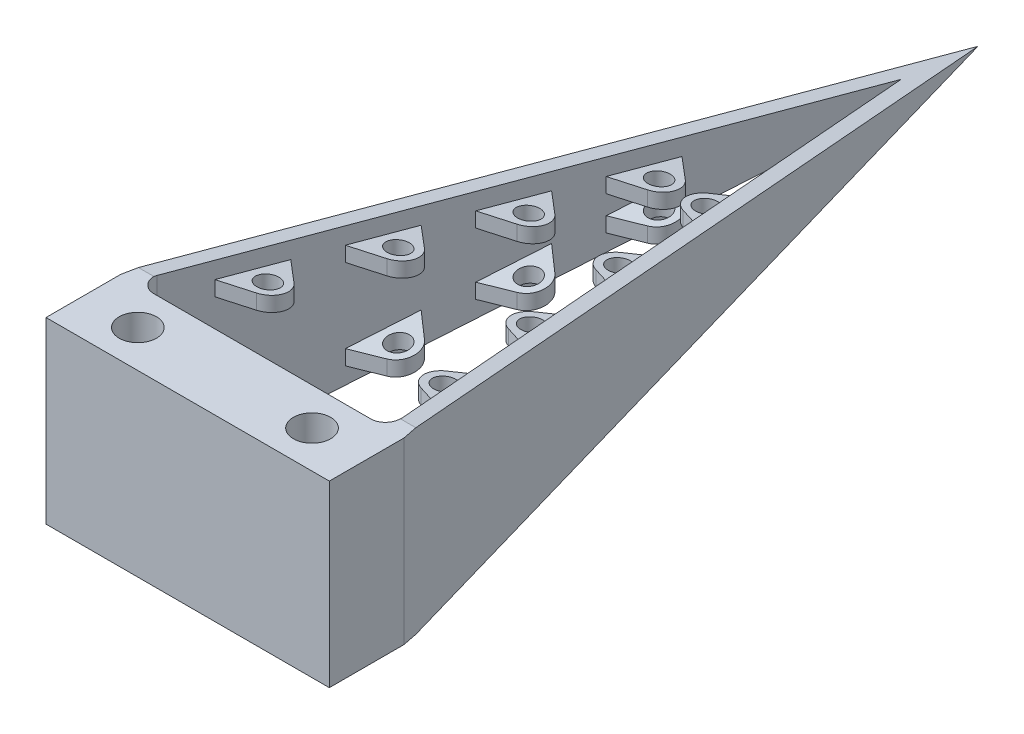
SolidWorks part; units mm, degrees
ref_plane "Front Plane" through (0, 0, 0) normal (0, 0, 1) x (1, 0, 0)
ref_plane "Top Plane" through (0, 0, 0) normal (0, 1, 0) x (1, 0, 0)
ref_plane "Right Plane" through (0, 0, 0) normal (1, 0, 0) x (0, 0, -1)
sketch "Sketch1" plane through (0, 0, 0) normal (0, 1, 0) x (1, 0, 0)
  line L0 (0, 152.4) -> (-30.1625, 0)
  line L1 (-30.1625, 0) -> (-30.1625, -15.875)
  line L2 (-30.1625, -15.875) -> (30.1625, -15.875)
  line L3 (30.1625, -15.875) -> (30.1625, 0)
  line L4 (30.1625, 0) -> (0, 152.4)
  line L5 (-30.1625, 0) -> (30.1625, 0) construction
  line L6 (0, 152.4) -> (0, 0) construction
  line L7 (-30.1625, -7.9375) -> (30.1625, -7.9375) construction
  line L8 (-26.9259, 0) -> (26.9259, 0)
  line L9 (26.9259, 0) -> (0, 136.0467)
  line L10 (0, 136.0467) -> (-26.9259, 0)
  circle A0 centre (-18.542, -7.9375) radius 3.9688
  circle A1 centre (18.542, -7.9375) radius 3.9688
  dimension "D1" = 7.9375
  dimension "D2" = 18.542
  dimension "D3" = 11.6205
  dimension "D4" = 7.9375
  dimension "D5" = 152.4
  dimension "D6" = 3.175
extrude "Boss-Extrude1" add sketch "Sketch1" along normal blind 34.925 and the other way blind 3.175
ref_plane "Plane1" through (0, 15.875, 0) normal (0, 1, 0) x (1, 0, 0)
fillet "Fillet1" radius 3.175 2 edges at (26.9259, 15.875, 0) (-26.9259, 15.875, 0)
sketch "Sketch2" plane through (0, 0, 0) normal (1, 0, 0) x (0, 0, -1)
  line L0 (3.175, 34.925) -> (152.4, 34.925)
  line L1 (0, 34.925) -> (152.4, 34.925) construction
  line L2 (152.4, 34.925) -> (152.4, 15.875)
  line L3 (152.4, -3.175) -> (152.4, 34.925) construction
  line L4 (152.4, 15.875) -> (3.175, 34.925)
  line L5 (3.175, -3.175) -> (152.4, -3.175)
  line L6 (0, -3.175) -> (152.4, -3.175) construction
  line L7 (152.4, -3.175) -> (152.4, 15.875)
  line L8 (3.175, -3.175) -> (152.4, 15.875)
  line L9 (0, -3.175) -> (0, 34.925) construction
  dimension "D1" = 3.175
extrude "Cut-Extrude1" cut sketch "Sketch2" against normal through all both and the other way through all contours L4 L2 L0 | L8 L5 L7
ref_plane "Plane2" through (0, 0, 0) normal (0, -0.9919, -0.1266) x (-1, 0, 0)
sketch "Sketch3" plane through (0, 0, 0) normal (0, -0.9919, -0.1266) x (-1, 0, 0)
  line L0 (-26.1755, 3.3688) -> (0, 136.6974) construction
  line L1 (-16.2187, 23.1834) -> (-24.1614, 30.114)
  line L2 (-17.543, 16.4381) -> (-27.5164, 13.0248)
  line L3 (-22.9287, 36.3928) -> (-19.5737, 53.482)
  line L4 (-24.1614, 30.114) -> (-27.5164, 13.0248)
  line L5 (-29.5341, 2.7474) -> (0, 153.1834) construction
  line L6 (-18.341, 59.7608) -> (-14.986, 76.85)
  line L7 (-13.7534, 83.1288) -> (-10.3984, 100.218)
  line L8 (-11.631, 46.5514) -> (-19.5737, 53.482)
  line L9 (-12.9553, 39.8061) -> (-22.9287, 36.3928)
  line L10 (-8.3676, 63.1741) -> (-18.341, 59.7608)
  line L11 (-14.986, 76.85) -> (-7.0433, 69.9194)
  line L12 (-13.7534, 83.1288) -> (-3.7799, 86.5421)
  line L13 (-10.3984, 100.218) -> (-2.4556, 93.2874)
  arc A0 (-17.543, 16.4381) -> (-16.2187, 23.1834) centre (-18.828, 20.193) ccw
  circle A1 centre (-18.828, 20.193) radius 3.9688 construction
  arc A2 (-12.9553, 39.8061) -> (-11.631, 46.5514) centre (-14.2403, 43.561) ccw
  circle A3 centre (-14.2403, 43.561) radius 2.3812
  arc A4 (-8.3676, 63.1741) -> (-7.0433, 69.9194) centre (-9.6527, 66.929) ccw
  circle A5 centre (-18.828, 20.193) radius 2.3813
  circle A6 centre (-9.6527, 66.929) radius 2.3812
  arc A7 (-3.7799, 86.5421) -> (-2.4556, 93.2874) centre (-5.065, 90.297) ccw
  circle A8 centre (-5.065, 90.297) radius 3.9687 construction
  circle A9 centre (-5.065, 90.297) radius 2.3812
  circle A10 centre (-14.2403, 43.561) radius 3.9687 construction
  circle A11 centre (-9.6527, 66.929) radius 3.9687 construction
  dimension "D1" = 20.193
  dimension "D6" = 7.9375
  dimension "D7" = 4.7625
  dimension "D2" = 23.368
  dimension "D3" = 23.368
  dimension "D4" = 23.368
  dimension "D5" = 60
  dimension "D8" = 60
  dimension "D9" = 60
  dimension "D10" = 60
  dimension "D11" = 60
  dimension "D12" = 60
  dimension "D13" = 60
extrude "Boss-Extrude9" add sketch "Sketch3" along direction (0, 1, 0) on the side against the normal blind 3.175
mirror "Mirror21" about plane through (0, 0, 0) normal (1, 0, 0) of "Boss-Extrude9"
mirror "Mirror22" about plane through (0, 15.875, 0) normal (0, 1, 0) of "Mirror21", "Boss-Extrude9"
